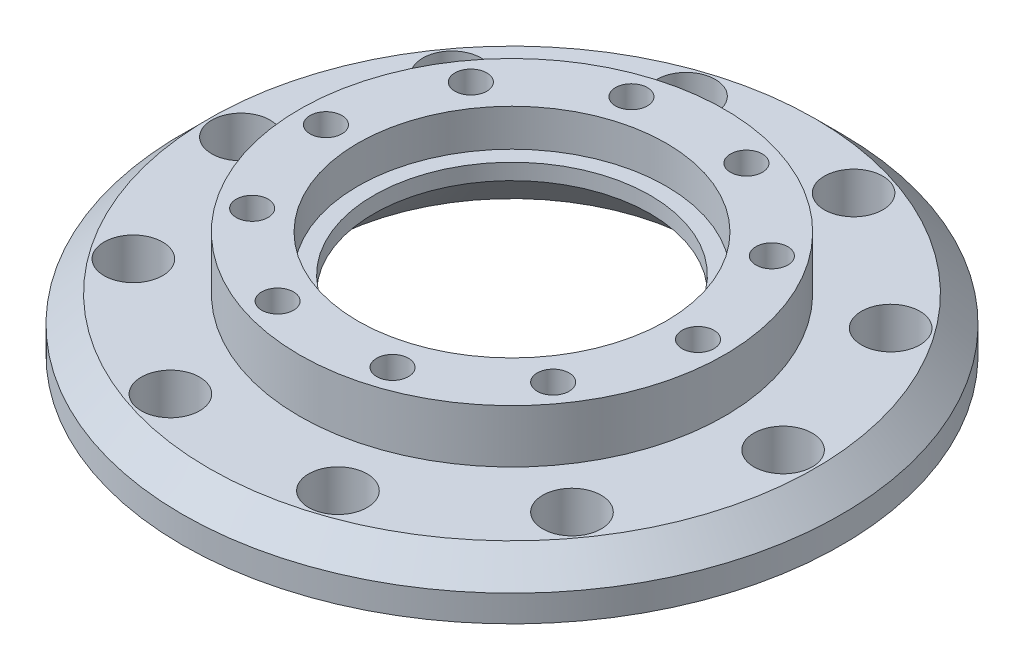
SolidWorks part; units mm, degrees
ref_plane "Front Plane" through (0, 0, 0) normal (0, 0, 1) x (1, 0, 0)
ref_plane "Top Plane" through (0, 0, 0) normal (0, 1, 0) x (1, 0, 0)
ref_plane "Right Plane" through (0, 0, 0) normal (1, 0, 0) x (0, 0, -1)
sketch "Sketch1" plane through (0, 0, 0) normal (0, 1, 0) x (1, 0, 0)
  line L0 (29, 0) -> (41, 0)
  circle A0 centre (0, 0) radius 51
  circle A1 centre (51, 0) radius 5.5
  circle A2 centre (41.2599, -29.977) radius 5.5
  circle A3 centre (15.7599, -48.5039) radius 5.5
  circle A4 centre (-15.7599, -48.5039) radius 5.5
  circle A5 centre (-41.2599, -29.977) radius 5.5
  circle A6 centre (-51, 0) radius 5.5
  circle A7 centre (-41.2599, 29.977) radius 5.5
  circle A8 centre (-15.7599, 48.5039) radius 5.5
  circle A9 centre (15.7599, 48.5039) radius 5.5
  circle A10 centre (41.2599, 29.977) radius 5.5
  circle A11 centre (0, 0) radius 41
  circle A12 centre (0, 0) radius 29
  circle A13 centre (35, 0) radius 3
  circle A14 centre (28.3156, -20.5725) radius 3
  circle A15 centre (10.8156, -33.287) radius 3
  circle A16 centre (-10.8156, -33.287) radius 3
  circle A17 centre (-28.3156, -20.5725) radius 3
  circle A18 centre (-35, 0) radius 3
  circle A19 centre (-28.3156, 20.5725) radius 3
  circle A20 centre (-10.8156, 33.287) radius 3
  circle A21 centre (10.8156, 33.287) radius 3
  circle A22 centre (28.3156, 20.5725) radius 3
  circle A23 centre (0, 0) radius 62
  point P25 (0, 0)
  point P50 (0, 0)
  dimension "D1" = 10
  dimension "D2" = 10
extrude "Boss-Extrude1" add sketch "Sketch1" along normal blind 10
sketch "Sketch2" plane through (0, 0, 0) normal (0, 1, 0) x (1, 0, 0)
  circle A0 centre (0, 0) radius 51
  circle A1 centre (51, 0) radius 5.5
  circle A2 centre (41.2599, -29.977) radius 5.5
  circle A3 centre (15.7599, -48.5039) radius 5.5
  circle A4 centre (-15.7599, -48.5039) radius 5.5
  circle A5 centre (-41.2599, -29.977) radius 5.5
  circle A6 centre (-51, 0) radius 5.5
  circle A7 centre (-41.2599, 29.977) radius 5.5
  circle A8 centre (-15.7599, 48.5039) radius 5.5
  circle A9 centre (15.7599, 48.5039) radius 5.5
  circle A10 centre (41.2599, 29.977) radius 5.5
  circle A11 centre (0, 0) radius 40
  circle A12 centre (0, 0) radius 29
  circle A13 centre (35, 0) radius 3
  circle A14 centre (28.3156, -20.5725) radius 3
  circle A15 centre (10.8156, -33.287) radius 3
  circle A16 centre (-10.8156, -33.287) radius 3
  circle A17 centre (-28.3156, -20.5725) radius 3
  circle A18 centre (-35, 0) radius 3
  circle A19 centre (-28.3156, 20.5725) radius 3
  circle A20 centre (-10.8156, 33.287) radius 3
  circle A21 centre (10.8156, 33.287) radius 3
  circle A22 centre (28.3156, 20.5725) radius 3
  circle A23 centre (0, 0) radius 62
  point P25 (0, 0)
  point P50 (0, 0)
  dimension "D1" = 10
  dimension "D2" = 10
extrude "Boss-Extrude2" add sketch "Sketch2" along normal blind 20
sketch "Sketch3" plane through (0, 20, 0) normal (0, 1, 0) x (1, 0, 0)
  circle A0 centre (-28.3156, -20.5725) radius 3
  circle A1 centre (-35, 0) radius 3
  circle A2 centre (-28.3156, 20.5725) radius 3
  circle A3 centre (-10.8156, 33.287) radius 3
  circle A4 centre (10.8156, 33.287) radius 3
  circle A5 centre (28.3156, 20.5725) radius 3
  circle A6 centre (35, 0) radius 3
  circle A7 centre (28.3156, -20.5725) radius 3
  circle A8 centre (10.8156, -33.287) radius 3
  circle A9 centre (-10.8156, -33.287) radius 3
  point P23 (0, 0)
  dimension "D1" = 10
extrude "Boss-Extrude3" add sketch "Sketch3" against normal blind 5 from offset 5 offset against normal yes
chamfer "Chamfer2" distance 5 angle 45 1 edges at (0, 10, 62)
chamfer "Chamfer3" distance 1 angle 45 10 edges at (41.2599, 0, 35.477) (51, 0, 5.5) (41.2599, 0, -24.477) (15.7599, 0, -43.0039) (-15.7599, 0, -43.0039) (-41.2599, 0, -24.477) (-51, 0, 5.5) (-41.2599, 0, 35.477) (-15.7599, 0, 54.0039) (15.7599, 0, 54.0039)
sketch "Sketch6" plane through (0, 0, 0) normal (0, -1, 0) x (1, 0, 0)
  circle A0 centre (0, 0) radius 29
  circle A1 centre (0, 0) radius 26
extrude "Boss-Extrude4" add sketch "Sketch6" against normal blind 13
chamfer "Chamfer4" distance 10 angle 45 1 edges at (0, 0, -26)
